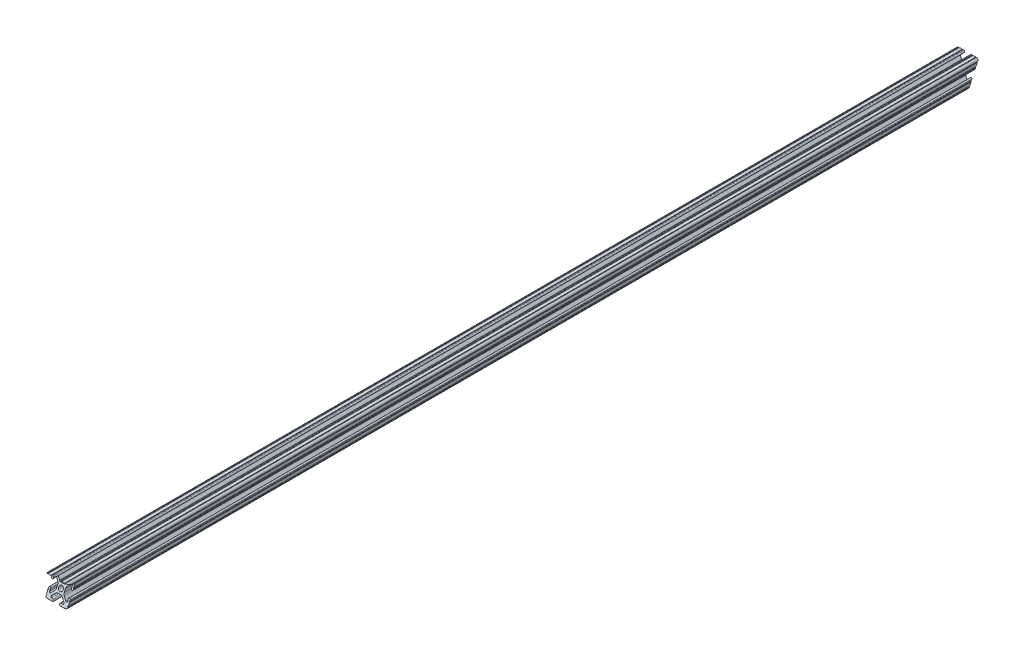
SolidWorks part; units mm, degrees
ref_plane "Front Plane" through (0, 0, 0) normal (0, 0, 1) x (1, 0, 0)
ref_plane "Top Plane" through (0, 0, 0) normal (0, 1, 0) x (1, 0, 0)
ref_plane "Right Plane" through (0, 0, 0) normal (1, 0, 0) x (0, 0, -1)
ref_plane "Plane1" through (0, 0, -450.85) normal (0, 0, -1) x (-1, 0, 0)
sketch "Sketch1" plane through (0, 0, -450.85) normal (0, 0, -1) x (-1, 0, 0)
  line L0 (12.7, -9.5504) -> (12.7, -6.3331)
  line L1 (12.7, -5.3171) -> (12.7, -4.3434)
  line L2 (10.4902, -4.3434) -> (10.4902, -6.4748)
  line L3 (8.7558, -7.1932) -> (5.4257, -3.8632)
  line L4 (4.4958, -1.6181) -> (4.4958, 1.6181)
  line L5 (5.4257, 3.8632) -> (8.7558, 7.1932)
  line L6 (10.4902, 6.4748) -> (10.4902, 4.3434)
  line L7 (12.7, 4.3434) -> (12.7, 5.3171)
  line L8 (12.7, 6.3331) -> (12.7, 9.5504)
  line L9 (9.5504, 12.7) -> (6.3331, 12.7)
  line L10 (5.3171, 12.7) -> (4.3434, 12.7)
  line L11 (4.3434, 10.4902) -> (6.4748, 10.4902)
  line L12 (7.1932, 8.7558) -> (3.8632, 5.4257)
  line L13 (1.6181, 4.4958) -> (-1.6181, 4.4958)
  line L14 (-3.8632, 5.4257) -> (-7.1932, 8.7558)
  line L15 (-6.4748, 10.4902) -> (-4.3434, 10.4902)
  line L16 (-4.3434, 12.7) -> (-5.3171, 12.7)
  line L17 (-6.3331, 12.7) -> (-9.5504, 12.7)
  line L18 (-12.7, 9.5504) -> (-12.7, 6.3331)
  line L19 (-12.7, 5.3171) -> (-12.7, 4.3434)
  line L20 (-10.4902, 4.3434) -> (-10.4902, 6.4748)
  line L21 (-8.7558, 7.1932) -> (-5.4257, 3.8632)
  line L22 (-4.4958, 1.6181) -> (-4.4958, -1.6181)
  line L23 (-5.4257, -3.8632) -> (-8.7558, -7.1932)
  line L24 (-10.4902, -6.4748) -> (-10.4902, -4.3434)
  line L25 (-12.7, -4.3434) -> (-12.7, -5.3171)
  line L26 (-12.7, -6.3331) -> (-12.7, -9.5504)
  line L27 (-9.5504, -12.7) -> (-6.3331, -12.7)
  line L28 (-5.3171, -12.7) -> (-4.3434, -12.7)
  line L29 (-4.3434, -10.4902) -> (-6.4748, -10.4902)
  line L30 (-7.1932, -8.7558) -> (-3.8632, -5.4257)
  line L31 (-1.6181, -4.4958) -> (1.6181, -4.4958)
  line L32 (3.8632, -5.4257) -> (7.1932, -8.7558)
  line L33 (6.4748, -10.4902) -> (4.3434, -10.4902)
  line L34 (4.3434, -12.7) -> (5.3171, -12.7)
  line L35 (6.3331, -12.7) -> (9.5504, -12.7)
  arc A0 (12.6998, -10.5664) -> (12.7, -9.5504) centre (12.7, -10.0584) cw
  arc A1 (12.7, -6.3331) -> (12.7, -5.3171) centre (12.7, -5.8251) cw
  arc A2 (12.7, -4.3434) -> (10.4902, -4.3434) centre (11.5951, -4.3434) ccw
  arc A3 (10.4902, -6.4748) -> (8.7558, -7.1932) centre (9.4742, -6.4748) cw
  arc A4 (5.4257, -3.8632) -> (4.4958, -1.6181) centre (7.6708, -1.6181) cw
  arc A5 (4.4958, 1.6181) -> (5.4257, 3.8632) centre (7.6708, 1.6181) cw
  arc A6 (8.7558, 7.1932) -> (10.4902, 6.4748) centre (9.4742, 6.4748) cw
  arc A7 (10.4902, 4.3434) -> (12.7, 4.3434) centre (11.5951, 4.3434) ccw
  arc A8 (12.7, 5.3171) -> (12.7, 6.3331) centre (12.7, 5.8251) cw
  arc A9 (12.7, 9.5504) -> (12.6998, 10.5664) centre (12.7, 10.0584) cw
  arc A10 (12.6998, 10.5664) -> (10.5664, 12.6998) centre (10.5918, 10.5918) ccw
  arc A11 (10.5664, 12.6998) -> (9.5504, 12.7) centre (10.0584, 12.7) cw
  arc A12 (6.3331, 12.7) -> (5.3171, 12.7) centre (5.8251, 12.7) cw
  arc A13 (4.3434, 12.7) -> (4.3434, 10.4902) centre (4.3434, 11.5951) ccw
  arc A14 (6.4748, 10.4902) -> (7.1932, 8.7558) centre (6.4748, 9.4742) cw
  arc A15 (3.8632, 5.4257) -> (1.6181, 4.4958) centre (1.6181, 7.6708) cw
  arc A16 (-1.6181, 4.4958) -> (-3.8632, 5.4257) centre (-1.6181, 7.6708) cw
  arc A17 (-7.1932, 8.7558) -> (-6.4748, 10.4902) centre (-6.4748, 9.4742) cw
  arc A18 (-4.3434, 10.4902) -> (-4.3434, 12.7) centre (-4.3434, 11.5951) ccw
  arc A19 (-5.3171, 12.7) -> (-6.3331, 12.7) centre (-5.8251, 12.7) cw
  arc A20 (-9.5504, 12.7) -> (-10.5664, 12.6998) centre (-10.0584, 12.7) cw
  arc A21 (-10.5664, 12.6998) -> (-12.6998, 10.5664) centre (-10.5918, 10.5918) ccw
  arc A22 (-12.6998, 10.5664) -> (-12.7, 9.5504) centre (-12.7, 10.0584) cw
  arc A23 (-12.7, 6.3331) -> (-12.7, 5.3171) centre (-12.7, 5.8251) cw
  arc A24 (-12.7, 4.3434) -> (-10.4902, 4.3434) centre (-11.5951, 4.3434) ccw
  arc A25 (-10.4902, 6.4748) -> (-8.7558, 7.1932) centre (-9.4742, 6.4748) cw
  arc A26 (-5.4257, 3.8632) -> (-4.4958, 1.6181) centre (-7.6708, 1.6181) cw
  arc A27 (-4.4958, -1.6181) -> (-5.4257, -3.8632) centre (-7.6708, -1.6181) cw
  arc A28 (-8.7558, -7.1932) -> (-10.4902, -6.4748) centre (-9.4742, -6.4748) cw
  arc A29 (-10.4902, -4.3434) -> (-12.7, -4.3434) centre (-11.5951, -4.3434) ccw
  arc A30 (-12.7, -5.3171) -> (-12.7, -6.3331) centre (-12.7, -5.8251) cw
  arc A31 (-12.7, -9.5504) -> (-12.6998, -10.5664) centre (-12.7, -10.0584) cw
  arc A32 (-12.6998, -10.5664) -> (-10.5664, -12.6998) centre (-10.5918, -10.5918) ccw
  arc A33 (-10.5664, -12.6998) -> (-9.5504, -12.7) centre (-10.0584, -12.7) cw
  arc A34 (-6.3331, -12.7) -> (-5.3171, -12.7) centre (-5.8251, -12.7) cw
  arc A35 (-4.3434, -12.7) -> (-4.3434, -10.4902) centre (-4.3434, -11.5951) ccw
  arc A36 (-6.4748, -10.4902) -> (-7.1932, -8.7558) centre (-6.4748, -9.4742) cw
  arc A37 (-3.8632, -5.4257) -> (-1.6181, -4.4958) centre (-1.6181, -7.6708) cw
  arc A38 (1.6181, -4.4958) -> (3.8632, -5.4257) centre (1.6181, -7.6708) cw
  arc A39 (7.1932, -8.7558) -> (6.4748, -10.4902) centre (6.4748, -9.4742) cw
  arc A40 (4.3434, -10.4902) -> (4.3434, -12.7) centre (4.3434, -11.5951) ccw
  arc A41 (5.3171, -12.7) -> (6.3331, -12.7) centre (5.8251, -12.7) cw
  arc A42 (9.5504, -12.7) -> (10.5664, -12.6998) centre (10.0584, -12.7) cw
  arc A43 (10.5664, -12.6998) -> (12.6998, -10.5664) centre (10.5918, -10.5918) ccw
  circle A44 centre (0, 0) radius 2.6035
extrude "Boss-Extrude1" add sketch "Sketch1" against normal mid plane 1078.1792
sketch "Sketch2" plane through (0, 0, 0) normal (1, 0, 0) x (0, 0, -1)
  line L0 (-88.2396, 12.6998) -> (-18.1943, -17.3795)
  line L2 (-88.2396, -12.6998) -> (-69.0361, 32.0189)
  line L3 (-88.2396, -12.6998) -> (989.9396, -12.6998) construction
  line L4 (974.659, 12.6998) -> (952.538, -34.8471)
  line L5 (952.538, -34.8471) -> (990.4424, -34.8471)
  line L6 (990.4424, -34.8471) -> (990.4424, 50.1289)
  line L7 (-88.2396, 12.6998) -> (989.9396, 12.6998) construction
  line L8 (-88.2396, 12.6998) -> (-101.0483, 21.6993)
  line L9 (-101.0483, 21.6993) -> (-97.3111, -6.0626)
  line L10 (990.4424, 50.1289) -> (974.659, 12.6998)
  line L11 (-97.3111, -6.0626) -> (-88.2396, -12.6998)
  line L12 (989.9396, 9.5504) -> (989.9396, 6.3331) construction
  point P12 (989.9396, 7.9417)
  dimension "D1" = 23.24
  dimension "D2" = 15.2806
  dimension "D3" = 66.76
  dimension "D4" = 65.05
extrude "Cut-Extrude2" cut sketch "Sketch2" against normal through all both and the other way through all
sketch "Sketch3" plane through (0, 0, 0) normal (1, 0, 0) x (0, 0, -1)
  line L0 (974.659, 12.6998) -> (972.6072, 8.2897)
  line L1 (973.1937, 9.5504) -> (971.6969, 6.3331) construction
  line L2 (972.6072, 8.2897) -> (963.1276, 12.7)
  line L3 (974.659, 12.7) -> (-88.2396, 12.7) construction
  line L4 (963.1276, 12.7) -> (944.5281, 17.5194)
  line L6 (944.5281, 17.5194) -> (957.8355, 16.2937)
  line L7 (957.8355, 16.2937) -> (974.659, 12.6998)
  dimension "D1" = 4.8641
extrude "Cut-Extrude4" [suppressed] cut sketch "Sketch3" against normal through all both and the other way through all
